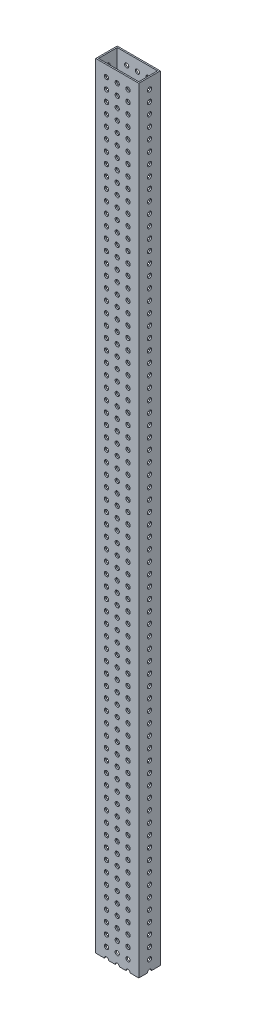
SolidWorks part; units mm, degrees
material "6061 Alloy"
ref_plane "Front Plane" through (0, 0, 0) normal (0, 0, 1) x (1, 0, 0)
ref_plane "Top Plane" through (0, 0, 0) normal (0, 1, 0) x (1, 0, 0)
ref_plane "Right Plane" through (0, 0, 0) normal (1, 0, 0) x (0, 0, -1)
sketch "Sketch1" plane through (0, 0, 0) normal (0, 1, 0) x (1, 0, 0)
  line L0 (1.5875, 1.5875) -> (49.2125, 1.5875)
  line L1 (0, 0) -> (50.8, 0)
  line L2 (0, 0) -> (0, 25.4)
  line L3 (0, 25.4) -> (50.8, 25.4)
  line L4 (50.8, 0) -> (50.8, 25.4)
  line L5 (49.2125, 1.5875) -> (49.2125, 23.8125)
  line L6 (1.5875, 23.8125) -> (49.2125, 23.8125)
  line L7 (1.5875, 1.5875) -> (1.5875, 23.8125)
  dimension "D2" = 50.8
  dimension "D3" = 25.4
  dimension "D1" = 1.5875
extrude "Boss-Extrude1" add sketch "Sketch1" along normal blind 914.4
sketch "Sketch3" plane through (50.8, 0, 0) normal (1, 0, 0) x (0, 0, -1)
  line L0 (0, 914.4) -> (25.4, 914.4) construction
  circle A0 centre (12.7, 901.7) radius 2.4892
  circle A1 centre (12.7, 889) radius 2.4892
  circle A2 centre (12.7, 876.3) radius 2.4892
  circle A3 centre (12.7, 863.6) radius 2.4892
  circle A4 centre (12.7, 850.9) radius 2.4892
  circle A5 centre (12.7, 838.2) radius 2.4892
  circle A6 centre (12.7, 825.5) radius 2.4892
  circle A7 centre (12.7, 812.8) radius 2.4892
  circle A8 centre (12.7, 800.1) radius 2.4892
  circle A9 centre (12.7, 787.4) radius 2.4892
  circle A10 centre (12.7, 774.7) radius 2.4892
  circle A11 centre (12.7, 762) radius 2.4892
  circle A12 centre (12.7, 749.3) radius 2.4892
  circle A13 centre (12.7, 736.6) radius 2.4892
  circle A14 centre (12.7, 723.9) radius 2.4892
  circle A15 centre (12.7, 711.2) radius 2.4892
  circle A16 centre (12.7, 698.5) radius 2.4892
  circle A17 centre (12.7, 685.8) radius 2.4892
  circle A18 centre (12.7, 673.1) radius 2.4892
  circle A19 centre (12.7, 660.4) radius 2.4892
  circle A20 centre (12.7, 647.7) radius 2.4892
  circle A21 centre (12.7, 635) radius 2.4892
  circle A22 centre (12.7, 622.3) radius 2.4892
  circle A23 centre (12.7, 609.6) radius 2.4892
  circle A24 centre (12.7, 596.9) radius 2.4892
  circle A25 centre (12.7, 584.2) radius 2.4892
  circle A26 centre (12.7, 571.5) radius 2.4892
  circle A27 centre (12.7, 558.8) radius 2.4892
  circle A28 centre (12.7, 546.1) radius 2.4892
  circle A29 centre (12.7, 533.4) radius 2.4892
  circle A30 centre (12.7, 520.7) radius 2.4892
  circle A31 centre (12.7, 508) radius 2.4892
  circle A32 centre (12.7, 495.3) radius 2.4892
  circle A33 centre (12.7, 482.6) radius 2.4892
  circle A34 centre (12.7, 469.9) radius 2.4892
  circle A35 centre (12.7, 457.2) radius 2.4892
  circle A36 centre (12.7, 444.5) radius 2.4892
  circle A37 centre (12.7, 431.8) radius 2.4892
  circle A38 centre (12.7, 419.1) radius 2.4892
  circle A39 centre (12.7, 406.4) radius 2.4892
  circle A40 centre (12.7, 393.7) radius 2.4892
  circle A41 centre (12.7, 381) radius 2.4892
  circle A42 centre (12.7, 368.3) radius 2.4892
  circle A43 centre (12.7, 355.6) radius 2.4892
  circle A44 centre (12.7, 342.9) radius 2.4892
  circle A45 centre (12.7, 330.2) radius 2.4892
  circle A46 centre (12.7, 317.5) radius 2.4892
  circle A47 centre (12.7, 304.8) radius 2.4892
  circle A48 centre (12.7, 292.1) radius 2.4892
  circle A49 centre (12.7, 279.4) radius 2.4892
  circle A50 centre (12.7, 266.7) radius 2.4892
  circle A51 centre (12.7, 254) radius 2.4892
  circle A52 centre (12.7, 241.3) radius 2.4892
  circle A53 centre (12.7, 228.6) radius 2.4892
  circle A54 centre (12.7, 215.9) radius 2.4892
  circle A55 centre (12.7, 203.2) radius 2.4892
  circle A56 centre (12.7, 190.5) radius 2.4892
  circle A57 centre (12.7, 177.8) radius 2.4892
  circle A58 centre (12.7, 165.1) radius 2.4892
  circle A59 centre (12.7, 152.4) radius 2.4892
  circle A60 centre (12.7, 139.7) radius 2.4892
  circle A61 centre (12.7, 127) radius 2.4892
  circle A62 centre (12.7, 114.3) radius 2.4892
  circle A63 centre (12.7, 101.6) radius 2.4892
  circle A64 centre (12.7, 88.9) radius 2.4892
  circle A65 centre (12.7, 76.2) radius 2.4892
  circle A66 centre (12.7, 63.5) radius 2.4892
  circle A67 centre (12.7, 50.8) radius 2.4892
  circle A68 centre (12.7, 38.1) radius 2.4892
  circle A69 centre (12.7, 25.4) radius 2.4892
  circle A70 centre (12.7, 12.7) radius 2.4892
  circle A71 centre (12.7, 0) radius 2.4892
  point P5 (12.7, 914.4)
  dimension "D1" = 4.9784
  dimension "D2" = 12.7
  dimension "D3" = 72
extrude "Cut-Extrude1" cut sketch "Sketch3" against normal through all
sketch "Sketch4" plane through (0, 0, 0) normal (0, 0, 1) x (1, 0, 0)
  line L0 (0, 914.4) -> (50.8, 914.4) construction
  line L1 (0, 914.4) -> (0, 0) construction
  line L2 (12.7, 901.7) -> (25.4, 901.7) construction
  line L3 (12.7, 901.7) -> (12.7, 889) construction
  circle A0 centre (12.7, 901.7) radius 2.4892
  circle A1 centre (25.4, 901.7) radius 2.4892
  circle A2 centre (38.1, 901.7) radius 2.4892
  circle A3 centre (25.4, 889) radius 2.4892
  circle A4 centre (38.1, 889) radius 2.4892
  circle A5 centre (25.4, 876.3) radius 2.4892
  circle A6 centre (38.1, 876.3) radius 2.4892
  circle A7 centre (25.4, 863.6) radius 2.4892
  circle A8 centre (38.1, 863.6) radius 2.4892
  circle A9 centre (25.4, 850.9) radius 2.4892
  circle A10 centre (38.1, 850.9) radius 2.4892
  circle A11 centre (25.4, 838.2) radius 2.4892
  circle A12 centre (38.1, 838.2) radius 2.4892
  circle A13 centre (25.4, 825.5) radius 2.4892
  circle A14 centre (38.1, 825.5) radius 2.4892
  circle A15 centre (25.4, 812.8) radius 2.4892
  circle A16 centre (38.1, 812.8) radius 2.4892
  circle A17 centre (25.4, 800.1) radius 2.4892
  circle A18 centre (38.1, 800.1) radius 2.4892
  circle A19 centre (25.4, 787.4) radius 2.4892
  circle A20 centre (38.1, 787.4) radius 2.4892
  circle A21 centre (25.4, 774.7) radius 2.4892
  circle A22 centre (38.1, 774.7) radius 2.4892
  circle A23 centre (25.4, 762) radius 2.4892
  circle A24 centre (38.1, 762) radius 2.4892
  circle A25 centre (25.4, 749.3) radius 2.4892
  circle A26 centre (38.1, 749.3) radius 2.4892
  circle A27 centre (25.4, 736.6) radius 2.4892
  circle A28 centre (38.1, 736.6) radius 2.4892
  circle A29 centre (25.4, 723.9) radius 2.4892
  circle A30 centre (38.1, 723.9) radius 2.4892
  circle A31 centre (25.4, 711.2) radius 2.4892
  circle A32 centre (38.1, 711.2) radius 2.4892
  circle A33 centre (25.4, 698.5) radius 2.4892
  circle A34 centre (38.1, 698.5) radius 2.4892
  circle A35 centre (25.4, 685.8) radius 2.4892
  circle A36 centre (38.1, 685.8) radius 2.4892
  circle A37 centre (25.4, 673.1) radius 2.4892
  circle A38 centre (38.1, 673.1) radius 2.4892
  circle A39 centre (25.4, 660.4) radius 2.4892
  circle A40 centre (38.1, 660.4) radius 2.4892
  circle A41 centre (25.4, 647.7) radius 2.4892
  circle A42 centre (38.1, 647.7) radius 2.4892
  circle A43 centre (25.4, 635) radius 2.4892
  circle A44 centre (38.1, 635) radius 2.4892
  circle A45 centre (25.4, 622.3) radius 2.4892
  circle A46 centre (38.1, 622.3) radius 2.4892
  circle A47 centre (25.4, 609.6) radius 2.4892
  circle A48 centre (38.1, 609.6) radius 2.4892
  circle A49 centre (25.4, 596.9) radius 2.4892
  circle A50 centre (38.1, 596.9) radius 2.4892
  circle A51 centre (25.4, 584.2) radius 2.4892
  circle A52 centre (38.1, 584.2) radius 2.4892
  circle A53 centre (25.4, 571.5) radius 2.4892
  circle A54 centre (38.1, 571.5) radius 2.4892
  circle A55 centre (25.4, 558.8) radius 2.4892
  circle A56 centre (38.1, 558.8) radius 2.4892
  circle A57 centre (25.4, 546.1) radius 2.4892
  circle A58 centre (38.1, 546.1) radius 2.4892
  circle A59 centre (25.4, 533.4) radius 2.4892
  circle A60 centre (38.1, 533.4) radius 2.4892
  circle A61 centre (25.4, 520.7) radius 2.4892
  circle A62 centre (38.1, 520.7) radius 2.4892
  circle A63 centre (25.4, 508) radius 2.4892
  circle A64 centre (38.1, 508) radius 2.4892
  circle A65 centre (25.4, 495.3) radius 2.4892
  circle A66 centre (38.1, 495.3) radius 2.4892
  circle A67 centre (25.4, 482.6) radius 2.4892
  circle A68 centre (38.1, 482.6) radius 2.4892
  circle A69 centre (25.4, 469.9) radius 2.4892
  circle A70 centre (38.1, 469.9) radius 2.4892
  circle A71 centre (25.4, 457.2) radius 2.4892
  circle A72 centre (38.1, 457.2) radius 2.4892
  circle A73 centre (25.4, 444.5) radius 2.4892
  circle A74 centre (38.1, 444.5) radius 2.4892
  circle A75 centre (25.4, 431.8) radius 2.4892
  circle A76 centre (38.1, 431.8) radius 2.4892
  circle A77 centre (25.4, 419.1) radius 2.4892
  circle A78 centre (38.1, 419.1) radius 2.4892
  circle A79 centre (25.4, 406.4) radius 2.4892
  circle A80 centre (38.1, 406.4) radius 2.4892
  circle A81 centre (25.4, 393.7) radius 2.4892
  circle A82 centre (38.1, 393.7) radius 2.4892
  circle A83 centre (25.4, 381) radius 2.4892
  circle A84 centre (38.1, 381) radius 2.4892
  circle A85 centre (25.4, 368.3) radius 2.4892
  circle A86 centre (38.1, 368.3) radius 2.4892
  circle A87 centre (25.4, 355.6) radius 2.4892
  circle A88 centre (38.1, 355.6) radius 2.4892
  circle A89 centre (25.4, 342.9) radius 2.4892
  circle A90 centre (38.1, 342.9) radius 2.4892
  circle A91 centre (25.4, 330.2) radius 2.4892
  circle A92 centre (38.1, 330.2) radius 2.4892
  circle A93 centre (25.4, 317.5) radius 2.4892
  circle A94 centre (38.1, 317.5) radius 2.4892
  circle A95 centre (25.4, 304.8) radius 2.4892
  circle A96 centre (38.1, 304.8) radius 2.4892
  circle A97 centre (25.4, 292.1) radius 2.4892
  circle A98 centre (38.1, 292.1) radius 2.4892
  circle A99 centre (25.4, 279.4) radius 2.4892
  circle A100 centre (38.1, 279.4) radius 2.4892
  circle A101 centre (25.4, 266.7) radius 2.4892
  circle A102 centre (38.1, 266.7) radius 2.4892
  circle A103 centre (25.4, 254) radius 2.4892
  circle A104 centre (38.1, 254) radius 2.4892
  circle A105 centre (25.4, 241.3) radius 2.4892
  circle A106 centre (38.1, 241.3) radius 2.4892
  circle A107 centre (25.4, 228.6) radius 2.4892
  circle A108 centre (38.1, 228.6) radius 2.4892
  circle A109 centre (25.4, 215.9) radius 2.4892
  circle A110 centre (38.1, 215.9) radius 2.4892
  circle A111 centre (25.4, 203.2) radius 2.4892
  circle A112 centre (38.1, 203.2) radius 2.4892
  circle A113 centre (25.4, 190.5) radius 2.4892
  circle A114 centre (38.1, 190.5) radius 2.4892
  circle A115 centre (25.4, 177.8) radius 2.4892
  circle A116 centre (38.1, 177.8) radius 2.4892
  circle A117 centre (25.4, 165.1) radius 2.4892
  circle A118 centre (38.1, 165.1) radius 2.4892
  circle A119 centre (25.4, 152.4) radius 2.4892
  circle A120 centre (38.1, 152.4) radius 2.4892
  circle A121 centre (25.4, 139.7) radius 2.4892
  circle A122 centre (38.1, 139.7) radius 2.4892
  circle A123 centre (25.4, 127) radius 2.4892
  circle A124 centre (38.1, 127) radius 2.4892
  circle A125 centre (25.4, 114.3) radius 2.4892
  circle A126 centre (38.1, 114.3) radius 2.4892
  circle A127 centre (25.4, 101.6) radius 2.4892
  circle A128 centre (38.1, 101.6) radius 2.4892
  circle A129 centre (25.4, 88.9) radius 2.4892
  circle A130 centre (38.1, 88.9) radius 2.4892
  circle A131 centre (25.4, 76.2) radius 2.4892
  circle A132 centre (38.1, 76.2) radius 2.4892
  circle A133 centre (25.4, 63.5) radius 2.4892
  circle A134 centre (38.1, 63.5) radius 2.4892
  circle A135 centre (25.4, 50.8) radius 2.4892
  circle A136 centre (38.1, 50.8) radius 2.4892
  circle A137 centre (25.4, 38.1) radius 2.4892
  circle A138 centre (38.1, 38.1) radius 2.4892
  circle A139 centre (25.4, 25.4) radius 2.4892
  circle A140 centre (38.1, 25.4) radius 2.4892
  circle A141 centre (25.4, 12.7) radius 2.4892
  circle A142 centre (38.1, 12.7) radius 2.4892
  circle A143 centre (25.4, 0) radius 2.4892
  circle A144 centre (38.1, 0) radius 2.4892
  circle A145 centre (12.7, 889) radius 2.4892
  circle A146 centre (12.7, 876.3) radius 2.4892
  circle A147 centre (12.7, 863.6) radius 2.4892
  circle A148 centre (12.7, 850.9) radius 2.4892
  circle A149 centre (12.7, 838.2) radius 2.4892
  circle A150 centre (12.7, 825.5) radius 2.4892
  circle A151 centre (12.7, 812.8) radius 2.4892
  circle A152 centre (12.7, 800.1) radius 2.4892
  circle A153 centre (12.7, 787.4) radius 2.4892
  circle A154 centre (12.7, 774.7) radius 2.4892
  circle A155 centre (12.7, 762) radius 2.4892
  circle A156 centre (12.7, 749.3) radius 2.4892
  circle A157 centre (12.7, 736.6) radius 2.4892
  circle A158 centre (12.7, 723.9) radius 2.4892
  circle A159 centre (12.7, 711.2) radius 2.4892
  circle A160 centre (12.7, 698.5) radius 2.4892
  circle A161 centre (12.7, 685.8) radius 2.4892
  circle A162 centre (12.7, 673.1) radius 2.4892
  circle A163 centre (12.7, 660.4) radius 2.4892
  circle A164 centre (12.7, 647.7) radius 2.4892
  circle A165 centre (12.7, 635) radius 2.4892
  circle A166 centre (12.7, 622.3) radius 2.4892
  circle A167 centre (12.7, 609.6) radius 2.4892
  circle A168 centre (12.7, 596.9) radius 2.4892
  circle A169 centre (12.7, 584.2) radius 2.4892
  circle A170 centre (12.7, 571.5) radius 2.4892
  circle A171 centre (12.7, 558.8) radius 2.4892
  circle A172 centre (12.7, 546.1) radius 2.4892
  circle A173 centre (12.7, 533.4) radius 2.4892
  circle A174 centre (12.7, 520.7) radius 2.4892
  circle A175 centre (12.7, 508) radius 2.4892
  circle A176 centre (12.7, 495.3) radius 2.4892
  circle A177 centre (12.7, 482.6) radius 2.4892
  circle A178 centre (12.7, 469.9) radius 2.4892
  circle A179 centre (12.7, 457.2) radius 2.4892
  circle A180 centre (12.7, 444.5) radius 2.4892
  circle A181 centre (12.7, 431.8) radius 2.4892
  circle A182 centre (12.7, 419.1) radius 2.4892
  circle A183 centre (12.7, 406.4) radius 2.4892
  circle A184 centre (12.7, 393.7) radius 2.4892
  circle A185 centre (12.7, 381) radius 2.4892
  circle A186 centre (12.7, 368.3) radius 2.4892
  circle A187 centre (12.7, 355.6) radius 2.4892
  circle A188 centre (12.7, 342.9) radius 2.4892
  circle A189 centre (12.7, 330.2) radius 2.4892
  circle A190 centre (12.7, 317.5) radius 2.4892
  circle A191 centre (12.7, 304.8) radius 2.4892
  circle A192 centre (12.7, 292.1) radius 2.4892
  circle A193 centre (12.7, 279.4) radius 2.4892
  circle A194 centre (12.7, 266.7) radius 2.4892
  circle A195 centre (12.7, 254) radius 2.4892
  circle A196 centre (12.7, 241.3) radius 2.4892
  circle A197 centre (12.7, 228.6) radius 2.4892
  circle A198 centre (12.7, 215.9) radius 2.4892
  circle A199 centre (12.7, 203.2) radius 2.4892
  circle A200 centre (12.7, 190.5) radius 2.4892
  circle A201 centre (12.7, 177.8) radius 2.4892
  circle A202 centre (12.7, 165.1) radius 2.4892
  circle A203 centre (12.7, 152.4) radius 2.4892
  circle A204 centre (12.7, 139.7) radius 2.4892
  circle A205 centre (12.7, 127) radius 2.4892
  circle A206 centre (12.7, 114.3) radius 2.4892
  circle A207 centre (12.7, 101.6) radius 2.4892
  circle A208 centre (12.7, 88.9) radius 2.4892
  circle A209 centre (12.7, 76.2) radius 2.4892
  circle A210 centre (12.7, 63.5) radius 2.4892
  circle A211 centre (12.7, 50.8) radius 2.4892
  circle A212 centre (12.7, 38.1) radius 2.4892
  circle A213 centre (12.7, 25.4) radius 2.4892
  circle A214 centre (12.7, 12.7) radius 2.4892
  circle A215 centre (12.7, 0) radius 2.4892
  dimension "D1" = 4.9784
  dimension "D2" = 12.7
  dimension "D3" = 12.7
  dimension "D6" = 12.7
  dimension "D7" = 12.7
  dimension "D4" = 3
  dimension "D5" = 72
extrude "Cut-Extrude2" cut sketch "Sketch4" against normal through all
